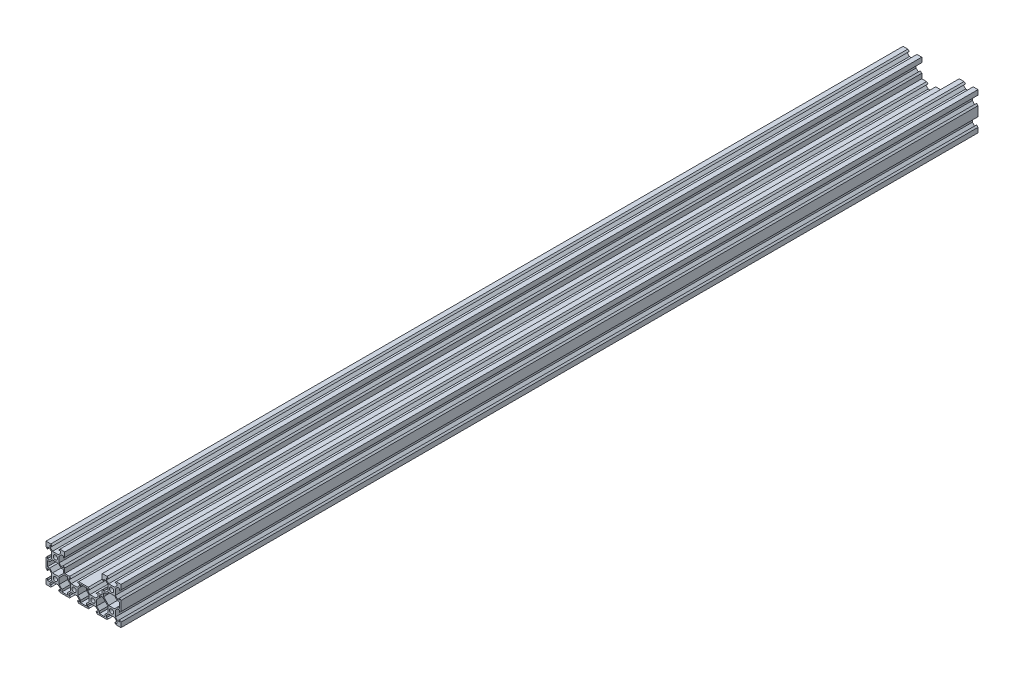
SolidWorks part; units mm, degrees
ref_plane "Front Plane" through (0, 0, 0) normal (0, 0, 1) x (1, 0, 0)
ref_plane "Top Plane" through (0, 0, 0) normal (0, 1, 0) x (1, 0, 0)
ref_plane "Right Plane" through (0, 0, 0) normal (1, 0, 0) x (0, 0, -1)
sketch "Sketch2" plane through (0, 0, 0) normal (0, 0, 1) x (1, 0, 0)
  line L0 (0, 10) -> (0, -10) construction
  line L1 (0, -10) -> (-40, -10)
  line L2 (-40, -10) -> (-40, 30)
  line L3 (-40, 30) -> (-20, 30)
  line L4 (-20, 30) -> (-20, 10)
  line L5 (-20, 10) -> (0, 10)
  line L6 (-20, 10) -> (-40, -10) construction
  line L7 (-20, 10) -> (0, -10) construction
  line L8 (0, 10) -> (-20, -10) construction
  line L9 (-20, -10) -> (-40, 10) construction
  line L10 (-40, 10) -> (-20, 30) construction
  line L11 (-20, 30) -> (-19.842, 30.1306) construction
  line L12 (-40, 30) -> (-20, 10) construction
  line L13 (-35.5, 28.5) -> (-35.5, 25.5)
  line L14 (-40, 24.875) -> (-38.5, 23.375)
  line L15 (-40, 20) -> (-20, 20) construction
  line L16 (-40, 15.125) -> (-38.5, 16.625)
  line L17 (-30, 30) -> (-30, -10) construction
  line L18 (-33.375, 28.5) -> (-35.5, 28.5)
  line L19 (-38.5, 25.5) -> (-35.5, 25.5)
  line L20 (-34.875, 30) -> (-33.375, 28.5)
  line L21 (-38.5, 23.375) -> (-38.5, 25.5)
  line L22 (-38.5, 16.625) -> (-38.5, 14.5)
  line L23 (-38.5, 14.5) -> (-35.5, 14.5)
  line L24 (-25.125, 30) -> (-26.625, 28.5)
  line L25 (-26.625, 28.5) -> (-24.5, 28.5)
  line L26 (-20, 24.875) -> (-21.5, 23.375)
  line L27 (-21.5, 23.375) -> (-21.5, 25.5)
  line L28 (-21.5, 25.5) -> (-24.5, 25.5)
  line L29 (-24.5, 28.5) -> (-24.5, 25.5)
  line L30 (-20, 15.125) -> (-21.5, 16.625)
  line L31 (-21.5, 16.625) -> (-21.5, 14.5)
  line L32 (-21.5, 14.5) -> (-24.5, 14.5)
  line L33 (-40, 4.875) -> (-38.5, 3.375)
  line L34 (-38.5, 3.375) -> (-38.5, 5.5)
  line L35 (-38.5, 5.5) -> (-35.5, 5.5)
  line L36 (-25.125, -10) -> (-26.625, -8.5)
  line L37 (-26.625, -8.5) -> (-24.5, -8.5)
  line L38 (-24.5, -8.5) -> (-24.5, -5.5)
  line L39 (-34.875, -10) -> (-33.375, -8.5)
  line L40 (-35.5, -8.5) -> (-35.5, -5.5)
  line L41 (-33.375, -8.5) -> (-35.5, -8.5)
  line L42 (-40, -4.875) -> (-38.5, -3.375)
  line L43 (-38.5, -3.375) -> (-38.5, -5.5)
  line L44 (-38.5, -5.5) -> (-35.5, -5.5)
  line L45 (-26, 24) -> (-34, 24)
  line L46 (-26, 24) -> (-26, 16)
  line L47 (-34, 24) -> (-34, 16)
  line L48 (-34, 16) -> (-26, 16)
  line L49 (-35.5, 26.3839) -> (-33.1161, 24)
  line L50 (-36.3839, 25.5) -> (-34, 23.1161)
  line L51 (-23.6161, 25.5) -> (-26, 23.1161)
  line L52 (-24.5, 26.3839) -> (-26.8839, 24)
  line L53 (-23.6161, 14.5) -> (-26, 16.8839)
  line L54 (-38.5, 13) -> (-38.5, 7)
  line L55 (-38.5, 13) -> (-36.1161, 13)
  line L56 (-36.3839, 14.5) -> (-34, 16.8839)
  line L57 (-36.1161, 13) -> (-33.1161, 16)
  line L58 (-38.5, 7) -> (-36.1161, 7)
  line L59 (-36.1161, 7) -> (-33.1161, 4)
  line L60 (-26, -4) -> (-34, -4)
  line L61 (-34, -4) -> (-34, 4)
  line L62 (-26, -4) -> (-26, 4)
  line L63 (-34, 4) -> (-26, 4)
  line L64 (-26.891, 4) -> (-21.5, 9.391)
  line L65 (-23.8839, 13) -> (-26.8839, 16)
  line L66 (-21.5, 13) -> (-23.8839, 13)
  line L67 (-21.5, 13) -> (-21.5, 9.391)
  line L68 (-23, -6.1161) -> (-26, -3.1161)
  line L69 (-23, -8.5) -> (-23, -6.1161)
  line L70 (-17, -8.5) -> (-23, -8.5)
  line L71 (-17, -8.5) -> (-17, -6.1161)
  line L72 (-17, -6.1161) -> (-14, -3.1161)
  line L73 (-17, 6.1161) -> (-14, 3.1161)
  line L74 (-17, 8.5) -> (-17, 6.1161)
  line L75 (-17, 8.5) -> (-20.609, 8.5)
  line L76 (-26, 3.109) -> (-20.609, 8.5)
  line L77 (-36.3839, 5.5) -> (-34, 3.1161)
  line L78 (-36.3839, -5.5) -> (-34, -3.1161)
  line L79 (-35.5, -6.3839) -> (-33.1161, -4)
  line L80 (-24.5, -6.3839) -> (-26.8839, -4)
  line L81 (-5.125, 10) -> (-6.625, 8.5)
  line L82 (-4.5, 8.5) -> (-4.5, 5.5)
  line L83 (-6.625, 8.5) -> (-4.5, 8.5)
  line L84 (-4.5, 6.3839) -> (-6.8839, 4)
  line L85 (14.875, -10) -> (13.375, -8.5)
  line L86 (-15.5, -8.5) -> (-15.5, -5.5)
  line L87 (-14.875, -10) -> (-13.375, -8.5)
  line L88 (-13.375, -8.5) -> (-15.5, -8.5)
  line L89 (13.375, -8.5) -> (15.5, -8.5)
  line L90 (15.5, -8.5) -> (15.5, -5.5)
  line L91 (-5.125, -10) -> (-6.625, -8.5)
  line L92 (-6.625, -8.5) -> (-4.5, -8.5)
  line L93 (-4.5, -8.5) -> (-4.5, -5.5)
  line L94 (-15.5, -6.3839) -> (-13.1161, -4)
  line L95 (15.5, -6.3839) -> (13.1161, -4)
  line L96 (4.5, -6.3839) -> (6.8839, -4)
  line L97 (-4.5, -6.3839) -> (-6.8839, -4)
  line L98 (-6, -4) -> (-6, 4)
  line L99 (-14, -4) -> (-6, -4)
  line L100 (-14, -4) -> (-14, 4)
  line L101 (-6, 4) -> (-14, 4)
  line L102 (0, 0) -> (-40, 0) construction
  line L103 (-15.5, 6.3839) -> (-13.1161, 4)
  line L104 (-15.5, 8.5) -> (-15.5, 5.5)
  line L105 (-14.875, 10) -> (-13.375, 8.5)
  line L106 (-13.375, 8.5) -> (-15.5, 8.5)
  line L107 (-10, 10) -> (-10, -10) construction
  line L108 (4.5, -8.5) -> (4.5, -5.5)
  line L109 (6.625, -8.5) -> (4.5, -8.5)
  line L110 (5.125, -10) -> (6.625, -8.5)
  line L111 (17, 8.5) -> (20.609, 8.5)
  line L112 (17, 8.5) -> (17, 6.1161)
  line L113 (17, 6.1161) -> (14, 3.1161)
  line L114 (15.5, 6.3839) -> (13.1161, 4)
  line L115 (14.875, 10) -> (13.375, 8.5)
  line L116 (15.5, 8.5) -> (15.5, 5.5)
  line L117 (13.375, 8.5) -> (15.5, 8.5)
  line L118 (5.125, 10) -> (6.625, 8.5)
  line L119 (6.625, 8.5) -> (4.5, 8.5)
  line L120 (4.5, 8.5) -> (4.5, 5.5)
  line L121 (4.5, 6.3839) -> (6.8839, 4)
  line L122 (14, -4) -> (6, -4)
  line L123 (14, -4) -> (14, 4)
  line L124 (6, 4) -> (14, 4)
  line L125 (6, -4) -> (6, 4)
  line L126 (0, -10) -> (40, -10)
  line L127 (36.3839, 14.5) -> (34, 16.8839)
  line L128 (40, 15.125) -> (38.5, 16.625)
  line L129 (38.5, 16.625) -> (38.5, 14.5)
  line L130 (38.5, 14.5) -> (35.5, 14.5)
  line L131 (38.5, 7) -> (36.1161, 7)
  line L132 (38.5, 13) -> (38.5, 7)
  line L133 (40, 4.875) -> (38.5, 3.375)
  line L134 (38.5, 3.375) -> (38.5, 5.5)
  line L135 (38.5, 5.5) -> (35.5, 5.5)
  line L136 (36.3839, 5.5) -> (34, 3.1161)
  line L137 (36.1161, 7) -> (33.1161, 4)
  line L138 (38.5, 13) -> (36.1161, 13)
  line L139 (36.1161, 13) -> (33.1161, 16)
  line L140 (26, 24) -> (34, 24)
  line L141 (34, 24) -> (34, 16)
  line L142 (34, 16) -> (26, 16)
  line L143 (26, 24) -> (26, 16)
  line L144 (23.6161, 14.5) -> (26, 16.8839)
  line L145 (21.5, 16.625) -> (21.5, 14.5)
  line L146 (20, 15.125) -> (21.5, 16.625)
  line L147 (21.5, 14.5) -> (24.5, 14.5)
  line L148 (23.8839, 13) -> (26.8839, 16)
  line L149 (21.5, 13) -> (23.8839, 13)
  line L150 (21.5, 13) -> (21.5, 9.391)
  line L151 (26.891, 4) -> (21.5, 9.391)
  line L152 (26, 3.109) -> (20.609, 8.5)
  line L153 (38.5, -3.375) -> (38.5, -5.5)
  line L154 (40, -4.875) -> (38.5, -3.375)
  line L155 (36.3839, -5.5) -> (34, -3.1161)
  line L156 (38.5, -5.5) -> (35.5, -5.5)
  line L157 (35.5, -6.3839) -> (33.1161, -4)
  line L158 (35.5, -8.5) -> (35.5, -5.5)
  line L159 (34.875, -10) -> (33.375, -8.5)
  line L160 (33.375, -8.5) -> (35.5, -8.5)
  line L161 (34, 4) -> (26, 4)
  line L162 (34, -4) -> (34, 4)
  line L163 (26, -4) -> (34, -4)
  line L164 (26, -4) -> (26, 4)
  line L165 (23, -6.1161) -> (26, -3.1161)
  line L166 (23, -8.5) -> (23, -6.1161)
  line L167 (26.625, -8.5) -> (24.5, -8.5)
  line L168 (24.5, -8.5) -> (24.5, -5.5)
  line L169 (24.5, -6.3839) -> (26.8839, -4)
  line L170 (17, -6.1161) -> (14, -3.1161)
  line L171 (17, -8.5) -> (17, -6.1161)
  line L172 (17, -8.5) -> (23, -8.5)
  line L173 (40, -10) -> (40, 30)
  line L174 (36.3839, 25.5) -> (34, 23.1161)
  line L175 (35.5, 26.3839) -> (33.1161, 24)
  line L176 (40, 24.875) -> (38.5, 23.375)
  line L177 (38.5, 23.375) -> (38.5, 25.5)
  line L178 (38.5, 25.5) -> (35.5, 25.5)
  line L179 (35.5, 28.5) -> (35.5, 25.5)
  line L180 (33.375, 28.5) -> (35.5, 28.5)
  line L181 (34.875, 30) -> (33.375, 28.5)
  line L182 (25.125, 30) -> (26.625, 28.5)
  line L183 (26.625, 28.5) -> (24.5, 28.5)
  line L184 (24.5, 26.3839) -> (26.8839, 24)
  line L185 (24.5, 28.5) -> (24.5, 25.5)
  line L186 (23.6161, 25.5) -> (26, 23.1161)
  line L187 (21.5, 25.5) -> (24.5, 25.5)
  line L188 (21.5, 23.375) -> (21.5, 25.5)
  line L189 (20, 24.875) -> (21.5, 23.375)
  line L190 (40, 30) -> (20, 30)
  line L191 (0, 10) -> (20, 10)
  line L192 (20, 10) -> (20, 30)
  line L193 (3, 8.5) -> (-3, 8.5)
  line L194 (-3, 8.5) -> (-3, 6.1161)
  line L195 (-3, 6.1161) -> (-6, 3.1161)
  line L196 (3, 8.5) -> (3, 6.1161)
  line L197 (3, 6.1161) -> (6, 3.1161)
  line L198 (-3, -8.5) -> (-3, -6.1161)
  line L199 (-3, -6.1161) -> (-6, -3.1161)
  line L200 (3, -6.1161) -> (6, -3.1161)
  line L201 (3, -8.5) -> (3, -6.1161)
  line L202 (3, -8.5) -> (-3, -8.5)
  line L203 (25.125, -10) -> (26.625, -8.5)
  circle A0 centre (-30, 20) radius 2.25
  circle A1 centre (-30, 0) radius 2.25
  circle A2 centre (-10, 0) radius 2.25
  circle A3 centre (10, 0) radius 2.25
  circle A4 centre (30, 20) radius 2.25
  circle A5 centre (30, 0) radius 2.25
  point P3 (0, 0)
  point P75 (-38.5, 10)
  point P232 (25.125, -10)
  point P271 (0, 8.5)
  dimension "D8" = 4.5
  dimension "D1" = 40
  dimension "D2" = 40
  dimension "D3" = 20
  dimension "D4" = 4.5
  dimension "D5" = 3.375
  dimension "D6" = 1.5
  dimension "D7" = 8
  dimension "D9" = 0.625
  dimension "D10" = 0.625
  dimension "D11" = 1.5
  dimension "D12" = 0.63
  dimension "D13" = 40
  dimension "D14" = 40
  dimension "D15" = 20
  dimension "D16" = 3
  dimension "D17" = 1.5
  dimension "D18" = 0.625
extrude "Boss-Extrude1" add sketch "Sketch2" along normal blind 914.4
